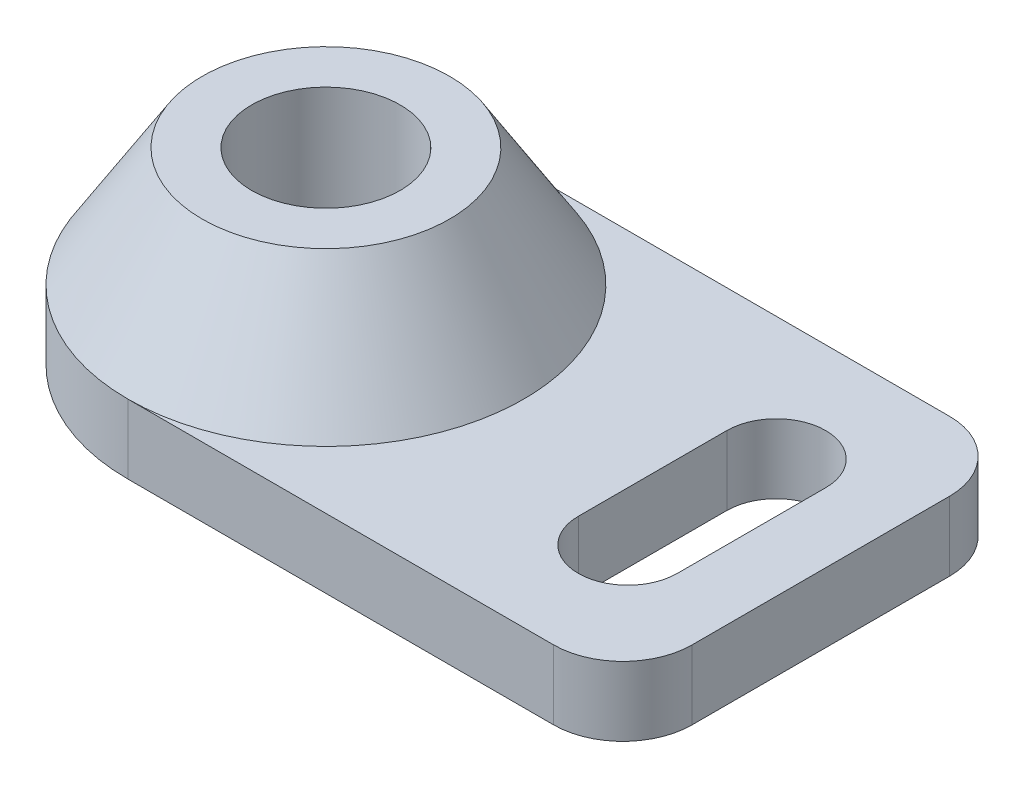
SolidWorks part; units mm, degrees
ref_plane "Front Plane" through (0, 0, 0) normal (0, 0, 1) x (1, 0, 0)
ref_plane "Top Plane" through (0, 0, 0) normal (0, 1, 0) x (1, 0, 0)
ref_plane "Right Plane" through (0, 0, 0) normal (1, 0, 0) x (0, 0, -1)
sketch "Sketch1" plane through (0, 0, 0) normal (0, 1, 0) x (1, 0, 0)
  line L1 (0, 0) -> (63.5, 0)
  line L3 (0, 50.8) -> (63.5, 50.8)
  line L4 (63.5, 0) -> (63.5, 50.8)
  arc A0 (0, 50.8) -> (0, 0) centre (0, 25.4) ccw
  dimension "D1" = 63.5
  dimension "D2" = 50.8
extrude "Boss-Extrude1" add sketch "Sketch1" along normal blind 8.89
sketch "Sketch2" plane through (0, 8.89, 0) normal (0, 1, 0) x (1, 0, 0)
  line L0 (48.26, 34.925) -> (48.26, 15.875) construction
  line L2 (41.91, 34.925) -> (41.91, 15.875)
  line L4 (54.61, 34.925) -> (54.61, 15.875)
  line L6 (63.5, 0) -> (63.5, 50.8) construction
  arc A0 (54.61, 34.925) -> (41.91, 34.925) centre (48.26, 34.925) ccw
  arc A1 (41.91, 15.875) -> (54.61, 15.875) centre (48.26, 15.875) ccw
  point P8 (63.5, 25.4)
  point P9 (54.61, 25.4)
  point P10 (0, 0)
  point P11 (0, 0)
  point P12 (0, 0)
  dimension "D1" = 12.7
  dimension "D2" = 15.24
  dimension "D3" = 19.05
extrude "Cut-Extrude2" cut sketch "Sketch2" against normal blind 8.89
fillet "Fillet1" radius 8.89 2 edges at (63.5, 4.445, -50.8) (63.5, 4.445, 0)
sketch "Sketch4" plane through (0, 8.89, 0) normal (0, 1, 0) x (1, 0, 0)
  line L0 (0, 50.8) -> (0, 0) construction
  circle A0 centre (0, 25.4) radius 25.4
  dimension "D1" = 50.8
ref_plane "Plane1" through (0, 24.13, 0) normal (0, 1, 0) x (1, 0, 0)
sketch "Sketch11" plane through (0, 24.13, 0) normal (0, 1, 0) x (1, 0, 0)
  circle A0 centre (0, 25.4) radius 15.875
  dimension "D1" = 31.75
loft "Loft2" add profiles "Sketch4", "Sketch11"
sketch "Sketch12" plane through (0, 24.13, 0) normal (0, 1, 0) x (1, 0, 0)
  circle A0 centre (0, 25.4) radius 9.525
  dimension "D1" = 19.05
extrude "Cut-Extrude3" cut sketch "Sketch12" against normal through all
